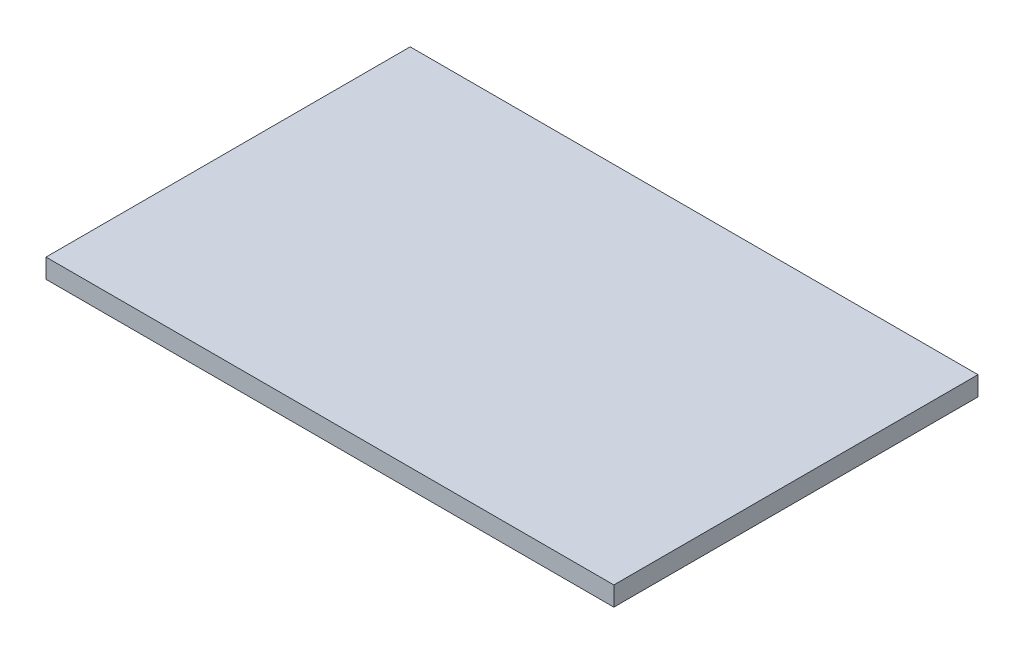
SolidWorks part; units mm, degrees
ref_plane "Front Plane" through (0, 0, 0) normal (0, 0, 1) x (1, 0, 0)
ref_plane "Top Plane" through (0, 0, 0) normal (0, 1, 0) x (1, 0, 0)
ref_plane "Right Plane" through (0, 0, 0) normal (1, 0, 0) x (0, 0, -1)
sketch "Sketch1" plane through (0, 0, 0) normal (0, 1, 0) x (1, 0, 0)
  line L1 (0, 0) -> (467.36, 0)
  line L2 (0, 0) -> (0, 299.72)
  line L3 (0, 299.72) -> (467.36, 299.72)
  line L4 (467.36, 0) -> (467.36, 299.72)
  dimension "D1" = 467.36
  dimension "D2" = 299.72
extrude "Boss-Extrude1" add sketch "Sketch1" along normal blind 15.875
